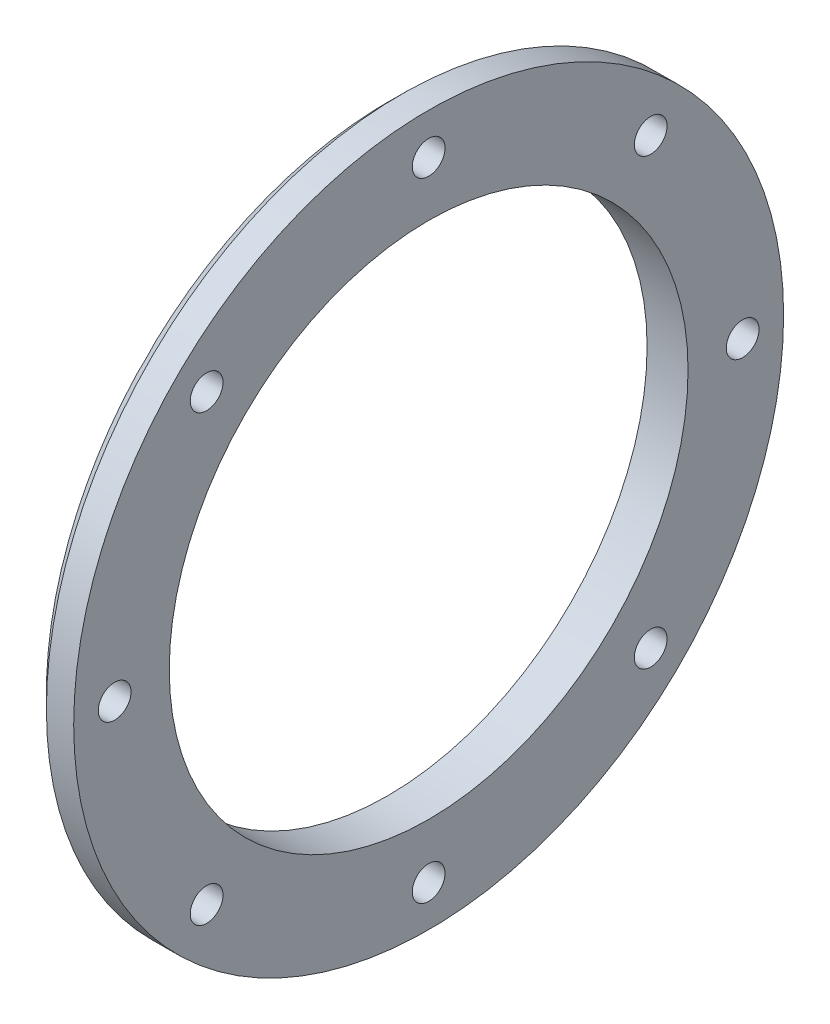
SolidWorks part; units mm, degrees
material "ПК/АБС"
ref_plane "Спереди" through (0, 0, 0) normal (0, 0, 1) x (1, 0, 0)
ref_plane "Сверху" through (0, 0, 0) normal (0, 1, 0) x (1, 0, 0)
ref_plane "Справа" through (0, 0, 0) normal (1, 0, 0) x (0, 0, -1)
sketch "Эскиз1" plane through (0, 0, 0) normal (0, 0, 1) x (1, 0, 0)
  line L5 (0, 19) -> (0, 25)
  line L6 (0, 25) -> (1, 26)
  line L7 (1, 26) -> (3, 26)
  line L8 (3, 26) -> (3, 19)
  line L9 (3, 19) -> (0, 19)
  line L10 (0, 0) -> (0, 19) construction
  line L11 (0, 0) -> (16163.9124, 0) construction
  point P7 (1.5, 19)
  dimension "D1" = 52
  dimension "D2" = 3
  dimension "D3" = 1
  dimension "D4" = 45
  dimension "D5" = 38
revolve "Повернуть1" add sketch "Эскиз1" angle 360 about L11
hole_wizard "Зенковка для винта с потайной головкой M21" positions "Эскиз2" profile "Эскиз3" countersink size "M2" standard "HASCO Metric" end condition through all
sketch "Эскиз2" plane through (0, 0, 0) normal (-1, 0, 0) x (0, 0, 1)
  line L0 (0, 0) -> (0, 25) construction
  line L2 (0, 0) -> (17.6777, 17.6777) construction
  circle A0 centre (0, 0) radius 25 construction
  circle A1 centre (0, 0) radius 23
  point P0 (16.2635, 16.2635)
  dimension "D2" = 46
  dimension "D1" = 45
sketch "Эскиз3" plane through (0, 16.2635, 16.2635) normal (0, 1, 0) x (0, 0, 1)
  line L0 (0, 0) -> (0, 3)
  line L1 (0, 3) -> (1.2, 3)
  line L2 (1.2, 3) -> (1.2, 1)
  line L3 (1.2, 1) -> (2.2, 0)
  line L5 (2.2, 0) -> (0, 0)
  line L6 (-1.2, 1) -> (-2.2, 0) construction
  line L11 (0, -6.35) -> (0, 107.95) construction
  dimension "Диаметр сквозного отверстия" = 2.4
  dimension "Глубина сквозного отверстия" = 3
  dimension "Диаметр передней зенковки" = 4.4
  dimension "Угол передней зенковки" = 90
pattern_circular "Круговой массив1" count 8 over 360 about axis through (0, 0, 0) along (1, 0, 0) of "Зенковка для винта с потайной головкой M21"
